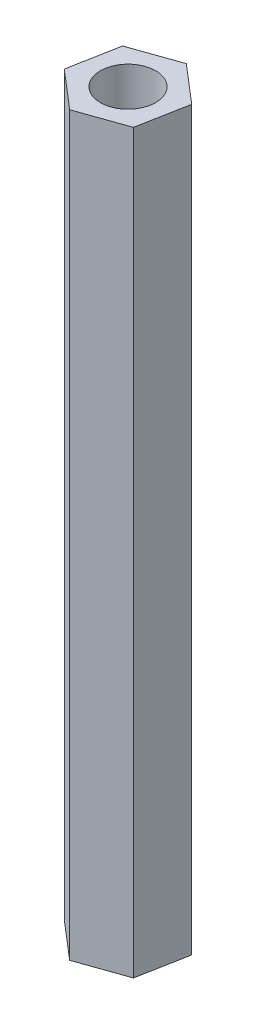
SolidWorks part; units mm, degrees
material "铜"
ref_plane "前视基准面" through (0, 0, 0) normal (0, 0, 1) x (1, 0, 0)
ref_plane "上视基准面" through (0, 0, 0) normal (0, 1, 0) x (1, 0, 0)
ref_plane "右视基准面" through (0, 0, 0) normal (1, 0, 0) x (0, 0, -1)
sketch "草图1" plane through (0, 0, 0) normal (0, 1, 0) x (1, 0, 0)
  line L1 (2.0609, -1.7652) -> (2.5592, 0.9022)
  line L2 (2.5592, 0.9022) -> (0.4983, 2.6674)
  line L3 (0.4983, 2.6674) -> (-2.0609, 1.7652)
  line L4 (-2.0609, 1.7652) -> (-2.5592, -0.9022)
  line L5 (-2.5592, -0.9022) -> (-0.4983, -2.6674)
  line L6 (-0.4983, -2.6674) -> (2.0609, -1.7652)
  circle A0 centre (0, 0) radius 2.35 construction
  circle A1 centre (0, 0) radius 1.5
  dimension "D1" = 4.7
  dimension "D2" = 3
extrude "凸台-拉伸1" add sketch "草图1" along normal blind 40
